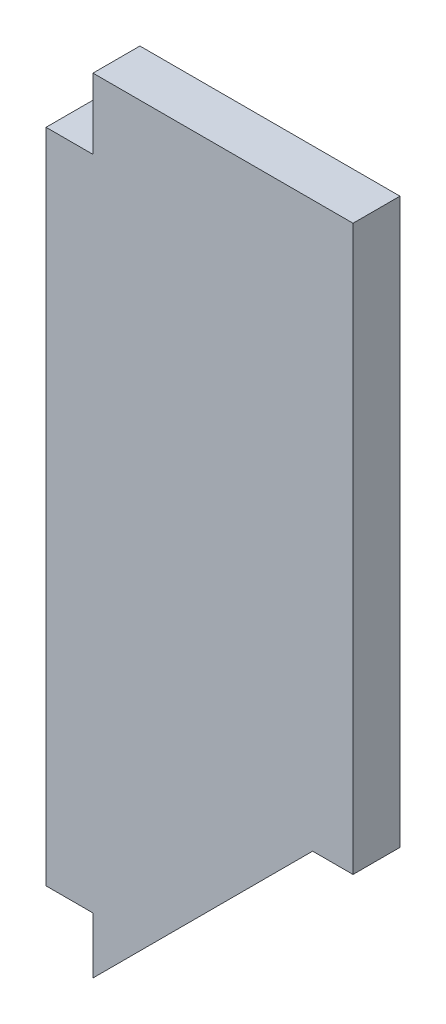
SolidWorks part; units mm, degrees
ref_plane "Front" through (0, 0, 0) normal (0, 0, 1) x (1, 0, 0)
ref_plane "Top" through (0, 0, 0) normal (0, 1, 0) x (1, 0, 0)
ref_plane "Right" through (0, 0, 0) normal (1, 0, 0) x (0, 0, -1)
sketch "Sketch1" plane through (0, 0, 0) normal (0, 0, 1) x (1, 0, 0)
  line L0 (0, -215.9) -> (8.89, -215.9)
  line L2 (0, 0) -> (0, -215.9)
  line L5 (8.89, -215.9) -> (72.1487, -152.6413)
  line L8 (76.7305, 0) -> (0, 0)
  line L9 (76.7305, 60.287) -> (76.7305, -158.2265) construction
  line L11 (72.1487, -152.6413) -> (83.0805, -152.6413)
  line L12 (76.7305, 0) -> (83.0805, 0)
  line L13 (83.0805, 0) -> (83.0805, -152.6413)
  line L14 (83.0805, 9.487) -> (83.0805, -160.8568) construction
  dimension "D1" = 215.9
  dimension "D2" = 8.89
  dimension "D3" = 135
extrude "Boss-Extrude1" add sketch "Sketch1" along normal blind 12.7
sketch "Sketch2" plane through (0, 0, 12.7) normal (0, 0, 1) x (1, 0, 0)
  line L1 (0, 0) -> (12.7, 0)
  line L2 (0, 0) -> (0, -19.05)
  line L3 (0, -19.05) -> (12.7, -19.05)
  line L4 (12.7, 0) -> (12.7, -19.05)
  line L5 (0, -215.9) -> (12.7, -215.9)
  line L6 (0, -215.9) -> (0, -196.85)
  line L7 (0, -196.85) -> (12.7, -196.85)
  line L8 (12.7, -215.9) -> (12.7, -196.85)
  dimension "D1" = 12.7
  dimension "D2" = 19.05
  dimension "D3" = 12.7
  dimension "D4" = 19.05
extrude "Cut-Extrude1" cut sketch "Sketch2" against normal through all
